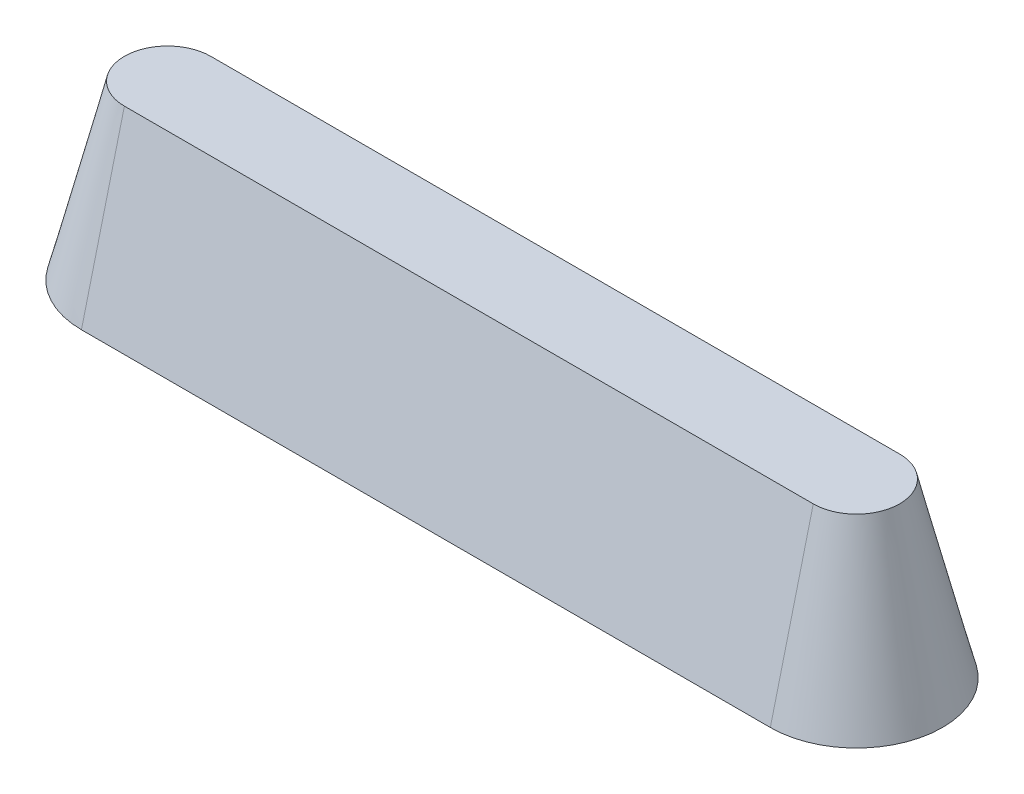
SolidWorks part; units mm, degrees
ref_plane "Alzado" through (0, 0, 0) normal (0, 0, 1) x (1, 0, 0)
ref_plane "Planta" through (0, 0, 0) normal (0, 1, 0) x (1, 0, 0)
ref_plane "Vista lateral" through (0, 0, 0) normal (1, 0, 0) x (0, 0, -1)
sketch "Croquis1" plane through (0, 0, 0) normal (0, 1, 0) x (1, 0, 0)
  line L0 (-157.1429, 0) -> (-37.1429, 0) construction
  line L1 (-157.1429, 15) -> (-37.1429, 15)
  line L2 (-157.1429, -15) -> (-37.1429, -15)
  arc A0 (-157.1429, 15) -> (-157.1429, -15) centre (-157.1429, 0) ccw
  arc A1 (-37.1429, -15) -> (-37.1429, 15) centre (-37.1429, 0) ccw
  point P3 (-97.1429, 0)
  dimension "D1" = 15
  dimension "D2" = 15
  dimension "D3" = 120
extrude "Saliente-Extruir1" add sketch "Croquis1" along normal blind 30 draft 14
